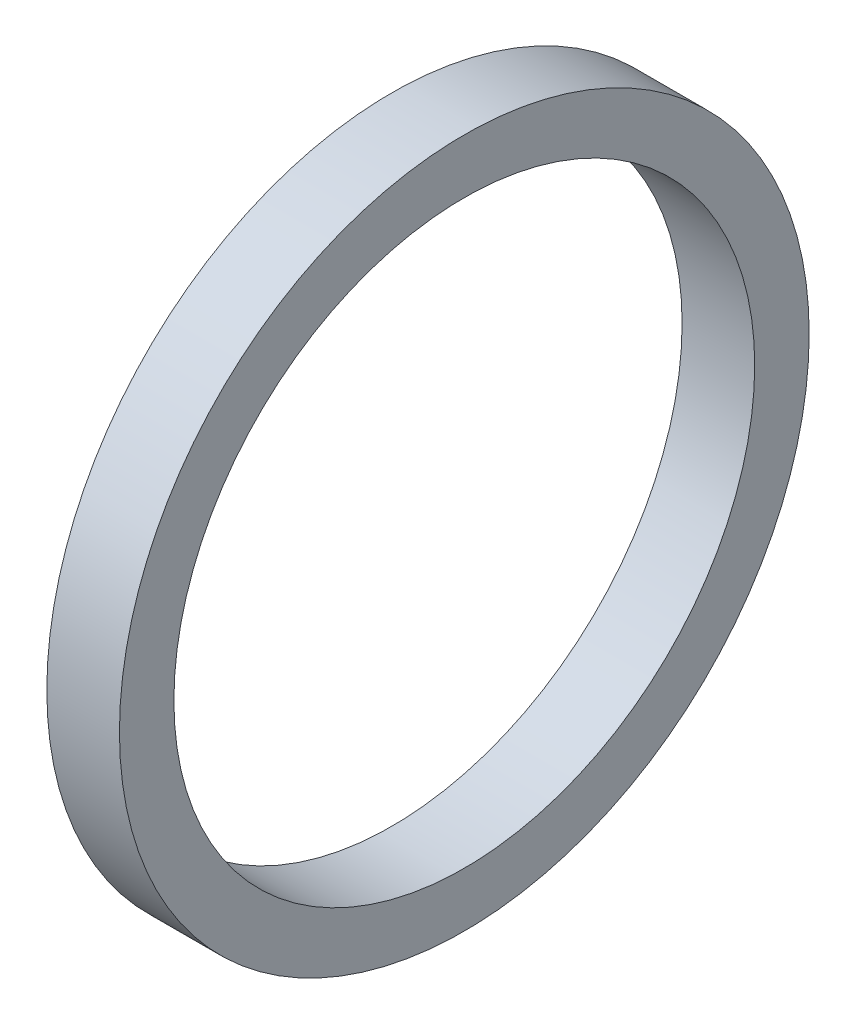
SolidWorks part; units mm, degrees
material "普通碳钢"
ref_plane "前视基准面" through (0, 0, 0) normal (0, 0, 1) x (1, 0, 0)
ref_plane "上视基准面" through (0, 0, 0) normal (0, 1, 0) x (1, 0, 0)
ref_plane "右视基准面" through (0, 0, 0) normal (1, 0, 0) x (0, 0, -1)
sketch "草图1" plane through (0, -928.7108, 3.0291) normal (0, 1, -0.0033) x (1, 0, 0)
  line L0 (4131.9132, -4952.6106) -> (4215.9132, -4952.6106) construction
  line L2 (4215.9132, -4971.6106) -> (4215.9132, -4933.6106) construction
  line L3 (4152.9132, -4925.1106) -> (4152.9132, -4980.1106) construction
  line L4 (4152.9132, -4936.6106) -> (4148.9132, -4936.6106)
  line L5 (4152.9132, -4936.6106) -> (4152.9132, -4933.6106)
  line L6 (4152.9132, -4933.6106) -> (4148.9132, -4933.6106)
  line L7 (4148.9132, -4936.6106) -> (4148.9132, -4933.6106)
  dimension "D1" = 16
  dimension "D2" = 3
  dimension "D3" = 4
revolve "旋转1" add sketch "草图1" angle 360 about L0
